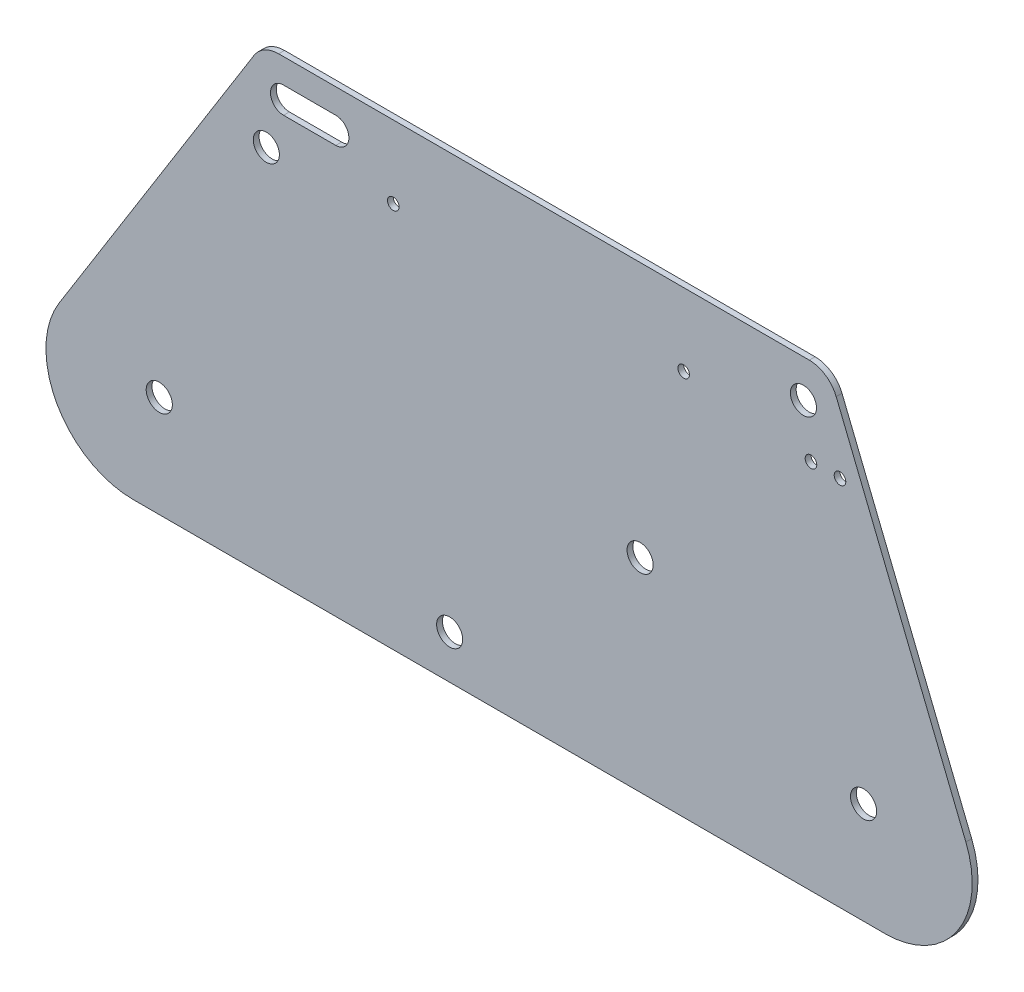
SolidWorks part; units mm, degrees
ref_plane "Front Plane" through (0, 0, 0) normal (0, 0, 1) x (1, 0, 0)
ref_plane "Top Plane" through (0, 0, 0) normal (0, 1, 0) x (1, 0, 0)
ref_plane "Right Plane" through (0, 0, 0) normal (1, 0, 0) x (0, 0, -1)
sketch "Sketch1" plane through (0, 0, 0) normal (0, 0, 1) x (1, 0, 0)
  line L0 (0, 0) -> (98.7294, 158)
  line L1 (0, 0) -> (357.5655, 0)
  line L3 (98.7294, 158) -> (293.7294, 158)
  line L5 (357.5655, 0) -> (293.7294, 158)
  line L6 (105.9354, 145) -> (123.9354, 145) construction
  line L7 (105.9354, 149.5) -> (123.9354, 149.5)
  line L8 (105.9354, 140.5) -> (123.9354, 140.5)
  arc A0 (105.9354, 149.5) -> (105.9354, 140.5) centre (105.9354, 145) ccw
  arc A1 (123.9354, 140.5) -> (123.9354, 149.5) centre (123.9354, 145) ccw
  circle A2 centre (284.9607, 145) radius 4.5
  circle A3 centre (305.6759, 35) radius 4.5
  circle A4 centre (63.1417, 35) radius 4.5
  circle A5 centre (163.1417, 15) radius 4.5
  circle A6 centre (228.7294, 70) radius 4.5
  circle A7 centre (100, 128) radius 4.5
  circle A8 centre (243.7294, 133) radius 2
  circle A9 centre (143.7294, 133) radius 2
  circle A10 centre (297.5655, 128) radius 2
  circle A11 centre (287.5655, 128) radius 2
  point P1 (114.9354, 145)
  dimension "D9" = 9
  dimension "D15" = 9
  dimension "D16" = 9
  dimension "D17" = 9
  dimension "D24" = 9
  dimension "D27" = 4
  dimension "D28" = 4
  dimension "D33" = 4
  dimension "D34" = 4
  dimension "D1" = 158
  dimension "D2" = 195
  dimension "D3" = 68
  dimension "D4" = 58
  dimension "D5" = 9
  dimension "D6" = 13
  dimension "D7" = 13
  dimension "D8" = 18
  dimension "D10" = 13
  dimension "D11" = 13
  dimension "D12" = 35
  dimension "D13" = 35
  dimension "D14" = 35
  dimension "D18" = 15
  dimension "D19" = 65
  dimension "D20" = 100
  dimension "D21" = 357.5655
  dimension "D22" = 70
  dimension "D23" = 65.5877
  dimension "D25" = 30
  dimension "D26" = 100
  dimension "D29" = 50
  dimension "D30" = 100
  dimension "D31" = 25
  dimension "D32" = 25
  dimension "D35" = 10
  dimension "D36" = 60
  dimension "D37" = 30
  dimension "D38" = 30
extrude "Boss-Extrude1" add sketch "Sketch1" along normal blind 2
fillet "Fillet1" radius 30 2 edges at (0, 0, 1) (357.5655, 0, 1)
fillet "Fillet2" radius 10 2 edges at (293.7294, 158, 1) (98.7294, 158, 1)
